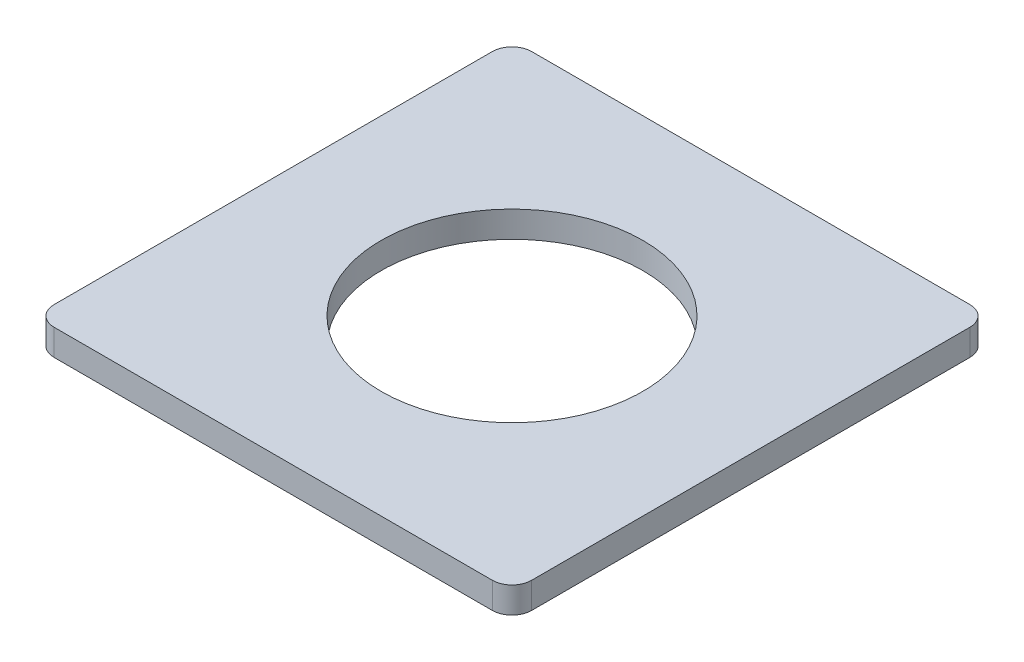
SolidWorks part; units mm, degrees
ref_plane "Front Plane" through (0, 0, 0) normal (0, 0, 1) x (1, 0, 0)
ref_plane "Top Plane" through (0, 0, 0) normal (0, 1, 0) x (1, 0, 0)
ref_plane "Right Plane" through (0, 0, 0) normal (1, 0, 0) x (0, 0, -1)
sketch "Sketch1" plane through (0, 0, 0) normal (0, 1, 0) x (1, 0, 0)
  line L1 (-9.271, -9.271) -> (9.271, -9.271)
  line L2 (-9.271, -9.271) -> (-9.271, 9.271)
  line L3 (-9.271, 9.271) -> (9.271, 9.271)
  line L4 (9.271, -9.271) -> (9.271, 9.271)
  line L5 (-9.271, -9.271) -> (9.271, 9.271) construction
  line L6 (-9.271, 9.271) -> (9.271, -9.271) construction
  circle A0 centre (0, 0) radius 5.08
  point P0 (0, 0)
  dimension "D2" = 10.16
  dimension "D1" = 18.542
extrude "Boss-Extrude1" add sketch "Sketch1" along normal blind 1.016
fillet "Fillet1" radius 0.762 4 edges at (9.271, 0.508, -9.271) (9.271, 0.508, 9.271) (-9.271, 0.508, -9.271) (-9.271, 0.508, 9.271)
